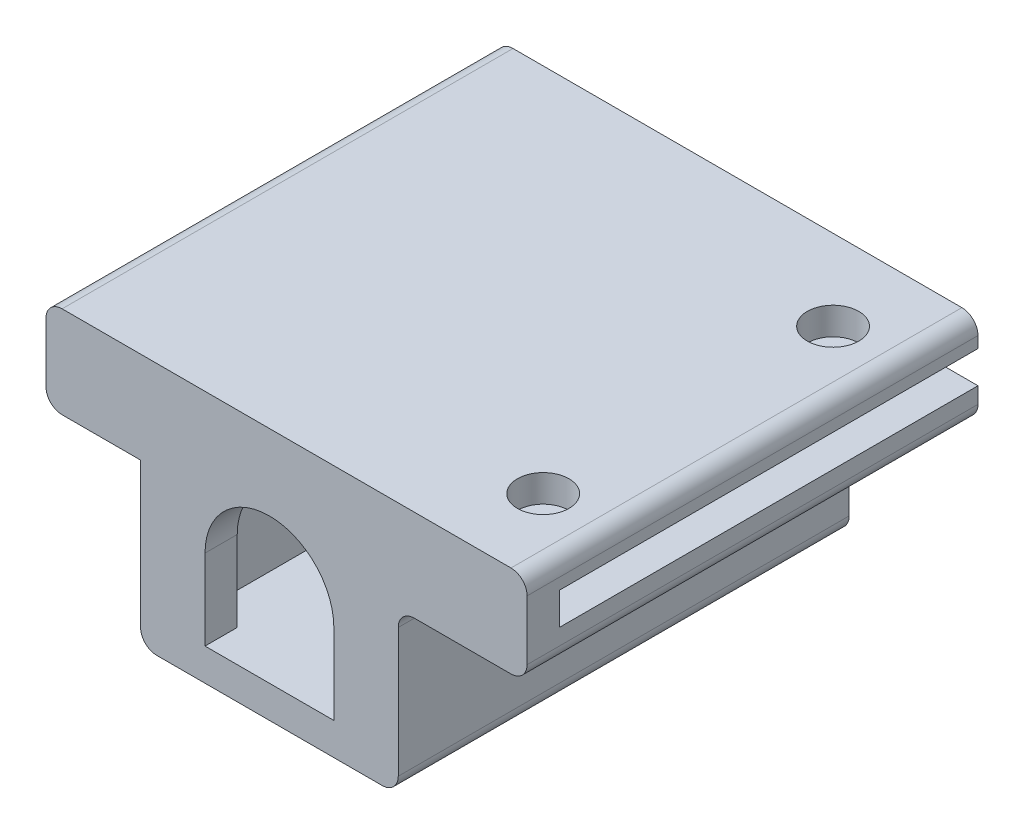
SolidWorks part; units mm, degrees
ref_plane "前视基准面" through (0, 0, 0) normal (0, 0, 1) x (1, 0, 0)
ref_plane "上视基准面" through (0, 0, 0) normal (0, 1, 0) x (1, 0, 0)
ref_plane "右视基准面" through (0, 0, 0) normal (1, 0, 0) x (0, 0, -1)
sketch "草图1" plane through (0, 0, 0) normal (0, 0, 1) x (1, 0, 0)
  line L0 (9, 3) -> (15, 3)
  line L1 (7, -7) -> (-7, -7)
  line L2 (8, -6) -> (8, 2)
  line L8 (6, -4) -> (6, 4)
  line L10 (-6, 4) -> (-6, -4)
  line L11 (-5, -5) -> (5, -5)
  line L19 (88.125, 5) -> (88.125, 7)
  line L20 (-8, -6) -> (-8, 3)
  line L21 (-12.875, 3) -> (-8, 3)
  line L22 (-13.875, 4) -> (-13.875, 7.7)
  line L23 (-12.875, 8.7) -> (15, 8.7)
  line L24 (16, 4) -> (16, 7.7)
  line L26 (4, 0) -> (4, -5)
  line L27 (4, -5) -> (-4, -5)
  line L28 (-4, 0) -> (-4, -5)
  line L29 (-5, 5) -> (5, 5)
  line L30 (-11.875, 5) -> (16, 5)
  line L31 (-11.875, 5) -> (-11.875, 6.7)
  line L32 (-11.875, 6.7) -> (16, 6.7)
  line L33 (16, 5) -> (16, 6.7)
  arc A0 (4, 0) -> (-4, 0) centre (0, 0) ccw
  arc A1 (15, 8.7) -> (16, 7.7) centre (15, 7.7) cw
  arc A2 (8, 2) -> (9, 3) centre (9, 2) cw
  arc A3 (16, 4) -> (15, 3) centre (15, 4) cw
  arc A8 (6, 4) -> (5, 5) centre (5, 4) ccw
  arc A9 (-5, 5) -> (-6, 4) centre (-5, 4) ccw
  arc A10 (-6, -4) -> (-5, -5) centre (-5, -4) ccw
  arc A11 (5, -5) -> (6, -4) centre (5, -4) ccw
  arc A12 (8, -6) -> (7, -7) centre (7, -6) cw
  arc A13 (-7, -7) -> (-8, -6) centre (-7, -6) cw
  arc A14 (-13.875, 7.7) -> (-12.875, 8.7) centre (-12.875, 7.7) cw
  arc A15 (-12.875, 3) -> (-13.875, 4) centre (-12.875, 4) cw
  dimension "D3" = 1
  dimension "D4" = 0
  dimension "D5" = 2
  dimension "D6" = 2
  dimension "D7" = 1.7
  dimension "D8" = 2
  dimension "D9" = 2
  dimension "D10" = 2
  dimension "D11" = 2
extrude "凸台-拉伸1" add sketch "草图1" along normal blind 2
sketch "草图2" plane through (0, 0, 0) normal (0, 0, -1) x (-1, 0, 0)
  line L1 (6, -5) -> (-6, -5)
  line L2 (6, -5) -> (6, 5)
  line L3 (6, 5) -> (-6, 5)
  line L4 (-6, 4) -> (-6, -4)
  line L5 (5, 5) -> (-5, 5)
  line L6 (6, -4) -> (6, 4)
  line L7 (-5, -5) -> (5, -5)
  line L8 (-6, 4) -> (-6, -4)
  line L9 (5, 5) -> (-5, 5)
  line L10 (6, -4) -> (6, 4)
  line L11 (-5, -5) -> (5, -5)
  line L12 (-16, 7.7) -> (-16, 4)
  line L13 (-15, 3) -> (-9, 3)
  line L14 (-8, 2) -> (-8, -6)
  line L15 (-7, -7) -> (7, -7)
  line L16 (8, -6) -> (8, 3)
  line L17 (8, 3) -> (12.875, 3)
  line L18 (13.875, 4) -> (13.875, 7.7)
  line L19 (12.875, 8.7) -> (-15, 8.7)
  line L23 (11.875, 7) -> (-88.125, 7)
  line L24 (-16, 7.7) -> (-16, 4)
  line L25 (-15, 3) -> (-9, 3)
  line L26 (-8, 2) -> (-8, -6)
  line L27 (-7, -7) -> (7, -7)
  line L28 (8, -6) -> (8, 3)
  line L29 (8, 3) -> (12.875, 3)
  line L30 (13.875, 4) -> (13.875, 7.7)
  line L31 (12.875, 8.7) -> (-15, 8.7)
  line L36 (-6, -5) -> (-6, 5)
  line L37 (11.875, 5) -> (11.875, 7)
  line L38 (-88.125, 5) -> (11.875, 5)
  line L39 (-88.125, 7) -> (-88.125, 5)
  line L40 (11.875, 7) -> (-88.125, 7)
  line L41 (11.875, 5) -> (11.875, 7)
  line L42 (-88.125, 5) -> (11.875, 5)
  line L43 (-88.125, 7) -> (-88.125, 5)
  arc A4 (-5, 5) -> (-6, 4) centre (-5, 4) ccw
  arc A5 (6, 4) -> (5, 5) centre (5, 4) ccw
  arc A6 (5, -5) -> (6, -4) centre (5, -4) ccw
  arc A7 (-6, -4) -> (-5, -5) centre (-5, -4) ccw
  arc A8 (-5, 5) -> (-6, 4) centre (-5, 4) ccw
  arc A9 (6, 4) -> (5, 5) centre (5, 4) ccw
  arc A10 (5, -5) -> (6, -4) centre (5, -4) ccw
  arc A11 (-6, -4) -> (-5, -5) centre (-5, -4) ccw
  arc A15 (-16, 4) -> (-15, 3) centre (-15, 4) ccw
  arc A16 (-16, 4) -> (-15, 3) centre (-15, 4) ccw
  arc A17 (-8, 2) -> (-9, 3) centre (-9, 2) ccw
  arc A18 (-8, 2) -> (-9, 3) centre (-9, 2) ccw
  arc A19 (-8, -6) -> (-7, -7) centre (-7, -6) ccw
  arc A20 (-8, -6) -> (-7, -7) centre (-7, -6) ccw
  arc A21 (7, -7) -> (8, -6) centre (7, -6) ccw
  arc A22 (7, -7) -> (8, -6) centre (7, -6) ccw
  arc A23 (12.875, 3) -> (13.875, 4) centre (12.875, 4) ccw
  arc A24 (12.875, 3) -> (13.875, 4) centre (12.875, 4) ccw
  arc A25 (13.875, 7.7) -> (12.875, 8.7) centre (12.875, 7.7) ccw
  arc A26 (13.875, 7.7) -> (12.875, 8.7) centre (12.875, 7.7) ccw
  arc A27 (-15, 8.7) -> (-16, 7.7) centre (-15, 7.7) ccw
  arc A28 (-15, 8.7) -> (-16, 7.7) centre (-15, 7.7) ccw
  dimension "D1" = 0
  dimension "D2" = 0
  dimension "D3" = 0
extrude "凸台-拉伸2" add sketch "草图2" along normal blind 26
sketch "草图4" plane through (0, 3, 0) normal (0, -1, 0) x (1, 0, 0)
  line L0 (12, -26) -> (12, 2) construction
  line L2 (12, -17.5359) -> (9, -19.2679)
  line L3 (9, -19.2679) -> (9, -22.7321)
  line L4 (9, 2) -> (9, -26)
  line L5 (9, -26) -> (15, -26)
  line L6 (15, -26) -> (15, 2)
  line L7 (15, 2) -> (9, 2)
  line L8 (9, 2) -> (9, -26)
  line L10 (15, -26) -> (15, 2)
  line L11 (15, 2) -> (9, 2)
  line L12 (9, -22.7321) -> (12, -24.4641)
  line L13 (12, -24.4641) -> (15, -22.7321)
  line L14 (15, -22.7321) -> (15, -19.2679)
  line L15 (15, -19.2679) -> (12, -17.5359)
  line L16 (15, -1.2679) -> (12, 0.4641)
  line L17 (12, 0.4641) -> (9, -1.2679)
  line L18 (9, -1.2679) -> (9, -4.7321)
  line L19 (9, -4.7321) -> (12, -6.4641)
  line L20 (12, -6.4641) -> (15, -4.7321)
  line L21 (15, -4.7321) -> (15, -1.2679)
  line L25 (9, -26) -> (15, -26)
  circle A0 centre (12, -21) radius 3 construction
  circle A1 centre (12, -3) radius 3 construction
  line M9 (9, 2) -> (9, -26)
  dimension "D2" = 6
  dimension "D3" = 6
  dimension "D5" = 5
  dimension "D1" = 0
sketch "草图6" plane through (0, 0, -26) normal (0, 0, -1) x (-1, 0, 0)
  line L1 (6, -5) -> (-6, -5)
  line L2 (6, -5) -> (6, -4)
  line L3 (6, -4) -> (-6, -4)
  line L4 (-6, -5) -> (-6, -4)
  line L16 (-6, 5) -> (-16, 5)
  line L17 (-16, 5) -> (-16, 4)
  line L18 (-15, 3) -> (-9, 3)
  line L19 (-8, 2) -> (-8, -6)
  line L20 (-7, -7) -> (7, -7)
  line L21 (8, -6) -> (8, 3)
  line L22 (8, 3) -> (12.875, 3)
  line L23 (13.875, 4) -> (13.875, 7.7)
  line L24 (12.875, 8.7) -> (-15, 8.7)
  line L25 (-16, 7.7) -> (-16, 7)
  line L26 (-16, 7) -> (11.875, 7)
  line L27 (11.875, 7) -> (11.875, 5)
  line L28 (11.875, 5) -> (6, 5)
  line L29 (6, 5) -> (6, -5)
  line L30 (6, -5) -> (-6, -5)
  line L31 (-6, -5) -> (-6, 5)
  line L32 (-6, 5) -> (-16, 5)
  line L33 (-16, 5) -> (-16, 4)
  line L34 (-15, 3) -> (-9, 3)
  line L35 (-8, 2) -> (-8, -6)
  line L36 (-7, -7) -> (7, -7)
  line L37 (8, -6) -> (8, 3)
  line L38 (8, 3) -> (12.875, 3)
  line L39 (13.875, 4) -> (13.875, 7.7)
  line L40 (12.875, 8.7) -> (-15, 8.7)
  line L41 (-16, 7.7) -> (-16, 7)
  line L42 (-16, 7) -> (11.875, 7)
  line L43 (11.875, 7) -> (11.875, 5)
  line L44 (11.875, 5) -> (6, 5)
  line L45 (6, 5) -> (6, -5)
  line L46 (6, -5) -> (-6, -5)
  line L47 (-6, -5) -> (-6, 5)
  arc A7 (-16, 4) -> (-15, 3) centre (-15, 4) ccw
  arc A8 (-8, 2) -> (-9, 3) centre (-9, 2) ccw
  arc A9 (-8, -6) -> (-7, -7) centre (-7, -6) ccw
  arc A10 (7, -7) -> (8, -6) centre (7, -6) ccw
  arc A11 (12.875, 3) -> (13.875, 4) centre (12.875, 4) ccw
  arc A12 (13.875, 7.7) -> (12.875, 8.7) centre (12.875, 7.7) ccw
  arc A13 (-15, 8.7) -> (-16, 7.7) centre (-15, 7.7) ccw
  arc A14 (-16, 4) -> (-15, 3) centre (-15, 4) ccw
  arc A15 (-8, 2) -> (-9, 3) centre (-9, 2) ccw
  arc A16 (-8, -6) -> (-7, -7) centre (-7, -6) ccw
  arc A17 (7, -7) -> (8, -6) centre (7, -6) ccw
  arc A18 (12.875, 3) -> (13.875, 4) centre (12.875, 4) ccw
  arc A19 (13.875, 7.7) -> (12.875, 8.7) centre (12.875, 7.7) ccw
  arc A20 (-15, 8.7) -> (-16, 7.7) centre (-15, 7.7) ccw
  line M46 (6, 5) -> (6, -5)
  line M47 (6, -5) -> (-6, -5)
  line M48 (-6, -5) -> (-6, 5)
  dimension "D2" = 1
  dimension "D1" = 0
extrude "凸台-拉伸3" add sketch "草图6" against normal blind 1.6 contours L3 M46 M48 M47
extrude "切除-拉伸1" cut sketch "草图4" against normal blind 1 and the other way through all contours L10 L15 L2 L12 L13 M9 | L19 L20 L10 L16 L17 L8
sketch "草图5" plane through (0, 4, 0) normal (0, -1, 0) x (1, 0, 0)
  line L0 (9, -19.2679) -> (15, -22.7321) construction
  line L1 (9, -1.2679) -> (15, -4.7321) construction
  line L6 (15, -22.7321) -> (15, -19.2679)
  line L7 (15, -19.2679) -> (12, -17.5359)
  line L8 (12, -17.5359) -> (9, -19.2679)
  line L9 (9, -19.2679) -> (9, -22.7321)
  line L10 (9, -22.7321) -> (12, -24.4641)
  line L11 (12, -24.4641) -> (15, -22.7321)
  line L12 (15, -22.7321) -> (15, -19.2679)
  line L13 (15, -19.2679) -> (12, -17.5359)
  line L14 (12, -17.5359) -> (9, -19.2679)
  line L15 (9, -19.2679) -> (9, -22.7321)
  line L16 (9, -22.7321) -> (12, -24.4641)
  line L17 (12, -24.4641) -> (15, -22.7321)
  line L18 (9, -4.7321) -> (12, -6.4641)
  line L19 (12, -6.4641) -> (15, -4.7321)
  line L20 (15, -4.7321) -> (15, -1.2679)
  line L21 (15, -1.2679) -> (12, 0.4641)
  line L22 (12, 0.4641) -> (9, -1.2679)
  line L23 (9, -1.2679) -> (9, -4.7321)
  line L24 (9, -4.7321) -> (12, -6.4641)
  line L25 (12, -6.4641) -> (15, -4.7321)
  line L26 (15, -4.7321) -> (15, -1.2679)
  line L27 (15, -1.2679) -> (12, 0.4641)
  line L28 (12, 0.4641) -> (9, -1.2679)
  line L29 (9, -1.2679) -> (9, -4.7321)
  circle A0 centre (12, -21) radius 1.6
  circle A1 centre (12, -3) radius 1.6
  dimension "D3" = 3.2
  dimension "D4" = 3.2
  dimension "D1" = 0
  dimension "D2" = 0
extrude "切除-拉伸2" cut sketch "草图5" against normal through all contours A0 | A1
